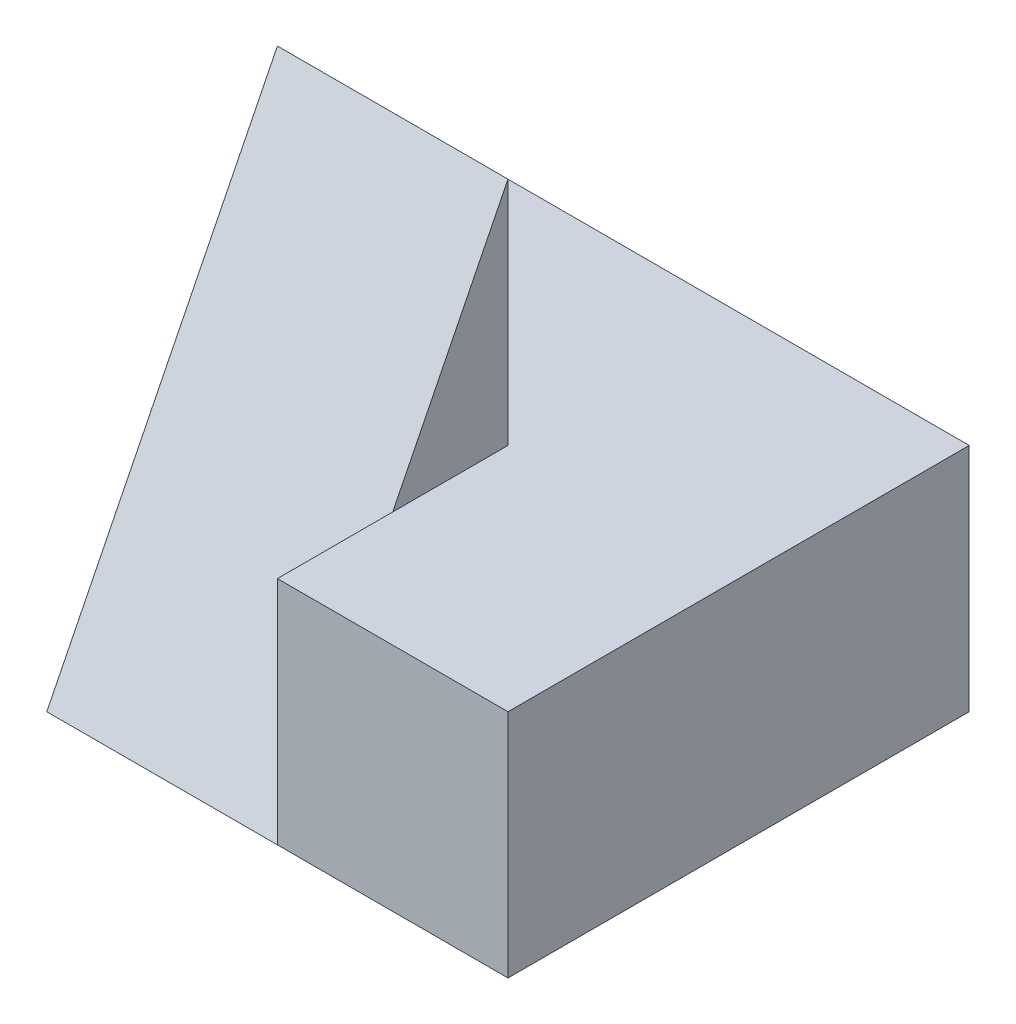
SolidWorks part; units mm, degrees
ref_plane "Front" through (0, 0, 0) normal (0, 0, 1) x (1, 0, 0)
ref_plane "Top" through (0, 0, 0) normal (0, 1, 0) x (1, 0, 0)
ref_plane "Right" through (0, 0, 0) normal (1, 0, 0) x (0, 0, -1)
sketch "Sketch1" plane through (0, 0, 0) normal (0, 1, 0) x (1, 0, 0)
  line L1 (0, 0) -> (4, 0)
  line L2 (0, 0) -> (0, 4)
  line L3 (0, 4) -> (4, 4)
  line L4 (4, 0) -> (4, 4)
  dimension "D1" = 4
  dimension "D2" = 4
extrude "Boss-Extrude1" add sketch "Sketch1" along normal blind 4
sketch "Sketch2" plane through (0, 4, 0) normal (0, 1, 0) x (1, 0, 0)
  line L0 (0, 0) -> (4, 0) construction
  line L5 (0, 2) -> (2, 2)
  line L6 (0, 2) -> (0, 0)
  line L7 (0, 0) -> (2, 0)
  line L8 (2, 2) -> (2, 0)
  line L9 (0, 4) -> (0, 0) construction
  line M1 (0, 4) -> (0, 0)
  line M2 (0, 0) -> (4, 0)
  line M3 (4, 0) -> (4, 4)
  line M4 (4, 4) -> (0, 4)
  dimension "D1" = 0
  dimension "D2" = 0
  dimension "D3" = 2
extrude "Cut-Extrude1" cut sketch "Sketch2" against normal blind 2 contours L8 L7 M4 M1 M2 M3
sketch "Sketch3" plane through (0, 0, 0) normal (-1, 0, 0) x (0, 0, 1)
  line L0 (0, 0) -> (-2, 4)
  line L1 (-2, 4) -> (0, 4)
  line L2 (0, 4) -> (0, 0)
extrude "Cut-Extrude2" cut sketch "Sketch3" against normal blind 2
